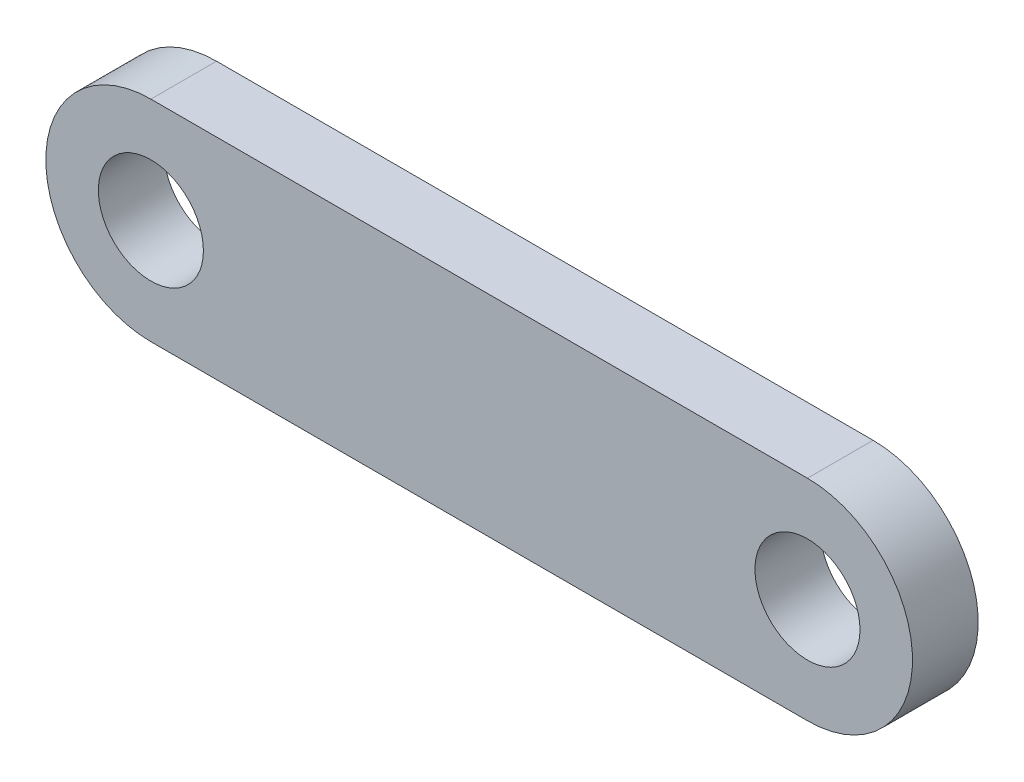
SolidWorks part; units mm, degrees
ref_plane "Front Plane" through (0, 0, 0) normal (0, 0, 1) x (1, 0, 0)
ref_plane "Top Plane" through (0, 0, 0) normal (0, 1, 0) x (1, 0, 0)
ref_plane "Right Plane" through (0, 0, 0) normal (1, 0, 0) x (0, 0, -1)
sketch "Sketch1" plane through (0, 0, 0) normal (0, 0, 1) x (1, 0, 0)
  line L0 (0, 8) -> (50, 8)
  line L1 (0, -8) -> (50, -8)
  circle A0 centre (0, 0) radius 4
  circle A1 centre (50, 0) radius 4
  arc A2 (0, 8) -> (0, -8) centre (0, 0) ccw
  arc A3 (50, -8) -> (50, 8) centre (50, 0) ccw
  dimension "D1" = 8
  dimension "D2" = 8
  dimension "D4" = 16
  dimension "D5" = 16
  dimension "D3" = 50
extrude "Boss-Extrude1" add sketch "Sketch1" against normal blind 5
